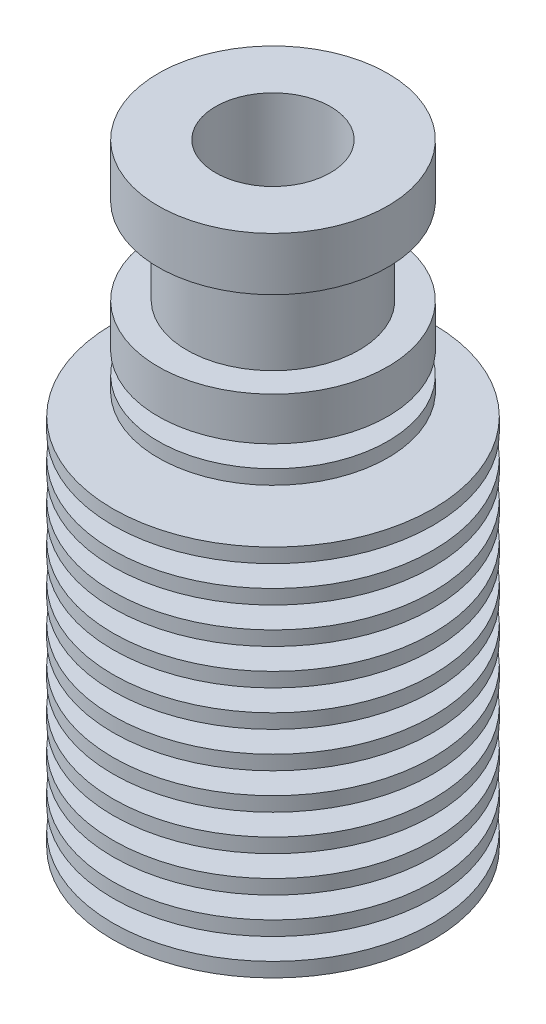
SolidWorks part; units mm, degrees
ref_plane "Спереди" through (0, 0, 0) normal (0, 0, 1) x (1, 0, 0)
ref_plane "Сверху" through (0, 0, 0) normal (0, 1, 0) x (1, 0, 0)
ref_plane "Справа" through (0, 0, 0) normal (1, 0, 0) x (0, 0, -1)
sketch "Эскиз1" plane through (0, 0, 0) normal (1, 0, 0) x (0, 0, -1)
  line L0 (0, 0) -> (0, 194.5212) construction
  line L1 (-4, 42.7) -> (-4, 34.7)
  line L2 (-4, 34.7) -> (-2.1, 33.603)
  line L3 (-2.1, 33.603) -> (-2.1, 0)
  line L4 (-4, 42.7) -> (-8, 42.7)
  line L5 (-8, 42.7) -> (-8, 39)
  line L6 (-8, 39) -> (-6, 39)
  line L7 (-6, 39) -> (-6, 33)
  line L8 (-6, 33) -> (-8, 33)
  line L9 (-8, 33) -> (-8, 30)
  line L10 (-8, 30) -> (-4, 30)
  line L11 (-4, 30) -> (-4, 28.5)
  line L12 (-4, 28.5) -> (-8, 28.5)
  line L13 (-8, 28.5) -> (-8, 27.5)
  line L14 (-8, 27.5) -> (-4, 27.5)
  line L15 (-4, 27.5) -> (-4, 26)
  line L16 (-4, 26) -> (-11.15, 26)
  line L17 (-11.15, 26) -> (-11.15, 25)
  line L18 (-11.15, 25) -> (-4, 25)
  line L19 (-2.1, 0) -> (-11.15, 0)
  line L20 (-11.15, 0) -> (-11.15, 1)
  line L21 (-11.15, 1) -> (-6.0997, 1)
  line L22 (-6.0997, 1) -> (-5.9685, 2.5)
  line L23 (-5.9685, 2.5) -> (-11.15, 2.5)
  line L24 (-11.15, 2.5) -> (-11.15, 3.5)
  line L25 (-11.15, 3.5) -> (-5.881, 3.5)
  line L26 (-5.881, 3.5) -> (-5.7498, 5)
  line L27 (-5.7498, 5) -> (-11.15, 5)
  line L28 (-11.15, 5) -> (-11.15, 6)
  line L29 (-11.15, 6) -> (-5.6623, 6)
  line L30 (-5.6623, 6) -> (-5.5311, 7.5)
  line L31 (-5.5311, 7.5) -> (-11.15, 7.5)
  line L32 (-11.15, 7.5) -> (-11.15, 8.5)
  line L33 (-11.15, 8.5) -> (-5.4436, 8.5)
  line L34 (-5.4436, 8.5) -> (-5.3123, 10)
  line L35 (-5.3123, 10) -> (-11.15, 10)
  line L36 (-11.15, 10) -> (-11.15, 11)
  line L37 (-11.15, 11) -> (-5.2248, 11)
  line L38 (-5.2248, 11) -> (-5.0936, 12.5)
  line L39 (-5.0936, 12.5) -> (-11.15, 12.5)
  line L40 (-11.15, 12.5) -> (-11.15, 13.5)
  line L41 (-11.15, 13.5) -> (-5.0061, 13.5)
  line L42 (-5.0061, 13.5) -> (-4.8749, 15)
  line L43 (-4.8749, 15) -> (-11.15, 15)
  line L44 (-11.15, 15) -> (-11.15, 16)
  line L45 (-11.15, 16) -> (-4.7874, 16)
  line L46 (-4.7874, 16) -> (-4.6562, 17.5)
  line L47 (-4.6562, 17.5) -> (-11.15, 17.5)
  line L48 (-11.15, 17.5) -> (-11.15, 18.5)
  line L49 (-11.15, 18.5) -> (-4.5687, 18.5)
  line L50 (-4.5687, 18.5) -> (-4.4374, 20)
  line L51 (-4.4374, 20) -> (-11.15, 20)
  line L52 (-11.15, 20) -> (-11.15, 21)
  line L53 (-11.15, 21) -> (-4.35, 21)
  line L54 (-4.35, 21) -> (-4.2187, 22.5)
  line L55 (-4.2187, 22.5) -> (-11.15, 22.5)
  line L56 (-11.15, 22.5) -> (-11.15, 23.5)
  line L57 (-11.15, 23.5) -> (-4.1312, 23.5)
  line L58 (-4.1312, 23.5) -> (-4, 25)
  dimension "D1" = 4.2
  dimension "D2" = 8
  dimension "D3" = 60
  dimension "D4" = 16
  dimension "D5" = 12
  dimension "D6" = 1
  dimension "D7" = 2.5
  dimension "D8" = 3.7
  dimension "D9" = 6
  dimension "D10" = 3
  dimension "D11" = 8
  dimension "D12" = 8
  dimension "D13" = 2.5
  dimension "D14" = 42.7
  dimension "D15" = 22.3
  dimension "D16" = 5
  dimension "D17" = 2.5
  dimension "D18" = 2.5
  dimension "D19" = 2.5
  dimension "D20" = 2.5
  dimension "D21" = 2.5
  dimension "D22" = 2.5
  dimension "D23" = 2.5
  dimension "D24" = 2.5
  dimension "D25" = 2.5
revolve "Повернуть1" add sketch "Эскиз1" angle 360 about L0
hole_wizard "Отверстие1" positions "Эскиз5" profile "Эскиз4" legacy
sketch "Эскиз5" plane through (0, 0, 0) normal (0, -1, 0) x (1, 0, 0)
  point P0 (0, 0)
sketch "Эскиз4" plane through (0, 0, 0) normal (1, 0, 0) x (0, 0, -1)
  line L0 (0, 0) -> (0, 16.5776)
  line L1 (0, 16.5776) -> (2.9585, 14.8)
  line L2 (2.9585, 14.8) -> (2.9585, 0)
  line L4 (2.9585, 0) -> (0, 0)
  line L6 (0, 16.5776) -> (-2.9585, 14.8) construction
  line L7 (0, -4.2442) -> (0, 117.3081) construction
  dimension "Диаметр" = 5.917
  dimension "Глубина" = 14.8
  dimension "Угол заточки сверла" = 118
cosmetic thread "Условное изображение резьбы1" parameters "D1"=10, "D2"=7
chamfer "Фаска1" distance 0.5 angle 45 1 edges at (0, 0, -2.9585)
